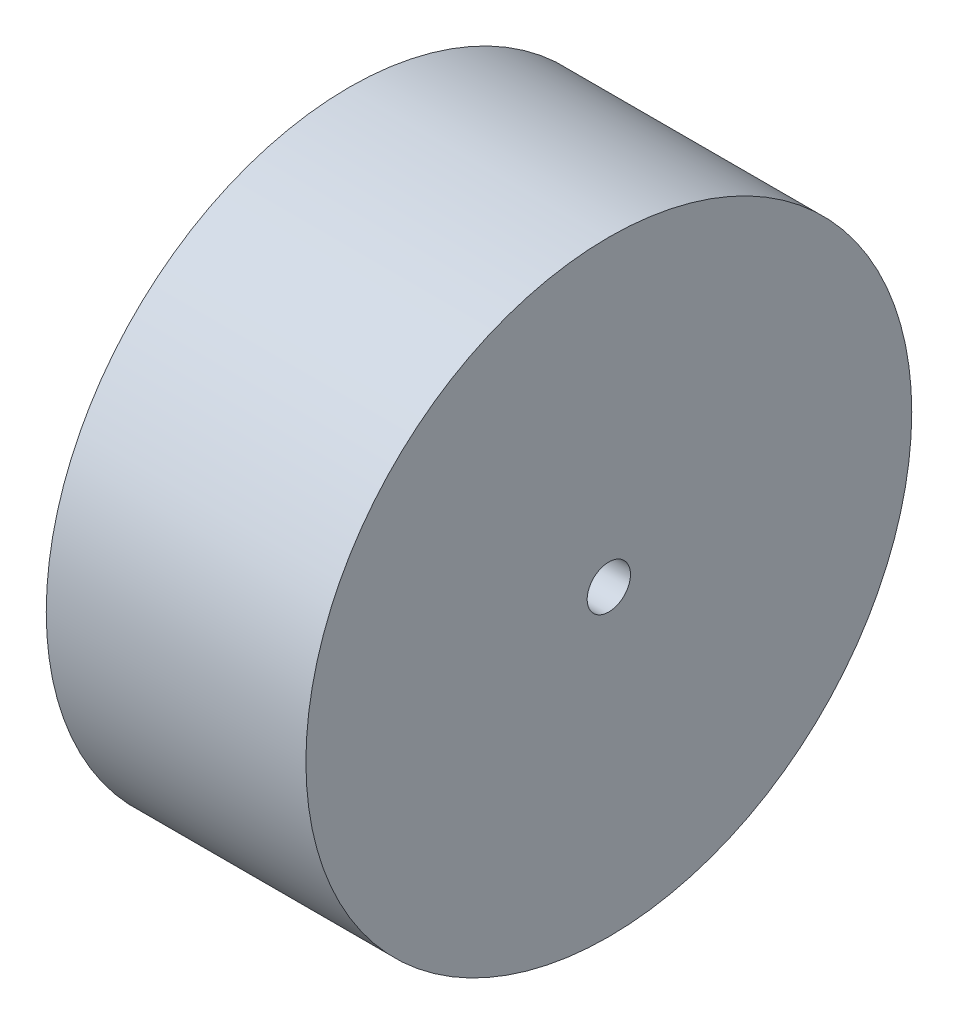
SolidWorks part; units mm, degrees
material "Силиконовая резина"
ref_plane "Спереди" through (0, 0, 0) normal (0, 0, 1) x (1, 0, 0)
ref_plane "Сверху" through (0, 0, 0) normal (0, 1, 0) x (1, 0, 0)
ref_plane "Справа" through (0, 0, 0) normal (1, 0, 0) x (0, 0, -1)
sketch "Эскиз1" plane through (0, 0, 0) normal (1, 0, 0) x (0, 0, -1)
  circle A0 centre (0, 0) radius 35
  circle A1 centre (0, 0) radius 2.5
  dimension "D1" = 70
  dimension "D2" = 5
extrude "колесо" add sketch "Эскиз1" along normal blind 30
